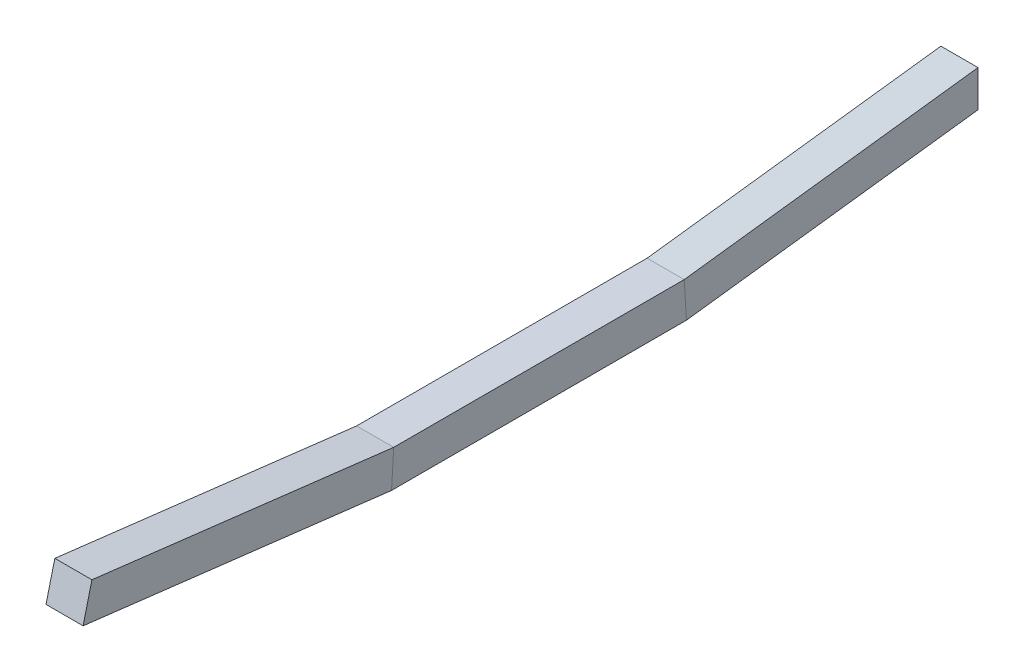
SolidWorks part; units mm, degrees
ref_plane "Front Plane" through (0, 0, 0) normal (0, 0, 1) x (1, 0, 0)
ref_plane "Top Plane" through (0, 0, 0) normal (0, 1, 0) x (1, 0, 0)
ref_plane "Right Plane" through (0, 0, 0) normal (1, 0, 0) x (0, 0, -1)
sketch3d "3DSketch1"
  line L0 (422.3508, 1821.5171, 1146.6546) -> (421.6447, 1770.7171, 1146.6546) construction
  line L1 (-923.8492, 1821.5171, 1146.6546) -> (1209.7508, 1821.5171, 1146.6546) construction
  line L2 (-923.8492, 1770.7171, 1146.6546) -> (1209.7508, 1770.7171, 1146.6546) construction
  line L3 (421.9978, 1796.1171, 1146.6546) -> (-34.8492, 1796.1171, 1146.6546) construction
  line L4 (409.1212, 1796.1171, 1146.6546) -> (409.1212, 1783.4171, 1146.6546) construction
  line L5 (-34.8492, 1796.1171, 1756.2546) -> (-34.8492, 1796.1171, 1146.6546) construction
  line L6 (409.1212, 1783.4171, 1146.6546) -> (421.8212, 1783.4171, 1146.6546) construction
  line L7 (409.1212, 1783.4171, 1146.6546) -> (409.1212, 1758.0171, 1146.6546) construction
  line L8 (409.1212, 1758.0171, 1146.6546) -> (409.1212, 1758.0171, 1764.8973) construction
  line L9 (409.1212, 1758.0171, 1764.8973) -> (409.1212, 1783.4171, 1764.8973) construction
  line L10 (409.1212, 1758.0171, 1349.8546) -> (409.1212, 1758.0171, 1553.0546)
  line L11 (421.6447, 1770.7171, 1146.6546) -> (421.9978, 1770.7171, 1146.6546)
  line L12 (409.1212, 1758.0171, 1349.8546) -> (409.1212, 1783.4171, 1146.6546)
  line L13 (409.1212, 1758.0171, 1553.0546) -> (409.1212, 1783.4171, 1764.8973)
  line L23 (421.6495, 1771.0606, 1146.6546) -> (421.9978, 1770.7171, 1146.6546) construction
  dimension "D1" = 457.2
  dimension "D2" = 457.2
  dimension "D3" = 12.7
  dimension "D4" = 12.7
  dimension "D5" = 25.4
  dimension "D6" = 213.36
  dimension "D7" = 25.4
  dimension "D8" = 203.2
  dimension "D9" = 203.2
sketch3d "3DSketch2"
  line L1 (396.2447, 1770.7171, 1146.6546) -> (421.9978, 1770.7171, 1146.6546)
  line L2 (396.2447, 1770.7171, 1146.6546) -> (396.2447, 1796.1171, 1146.6546)
  line L3 (396.2447, 1796.1171, 1146.6546) -> (421.9978, 1796.1171, 1146.6546)
  line L4 (421.9978, 1770.7171, 1146.6546) -> (421.9978, 1796.1171, 1146.6546)
  line L5 (396.2447, 1770.7171, 1146.6546) -> (421.9978, 1796.1171, 1146.6546) construction
  line L6 (396.2447, 1796.1171, 1146.6546) -> (421.9978, 1770.7171, 1146.6546) construction
  point P0 (409.1212, 1783.4171, 1146.6546)
sweep "Sweep1" add profiles "3DSketch2" path "3DSketch1"
